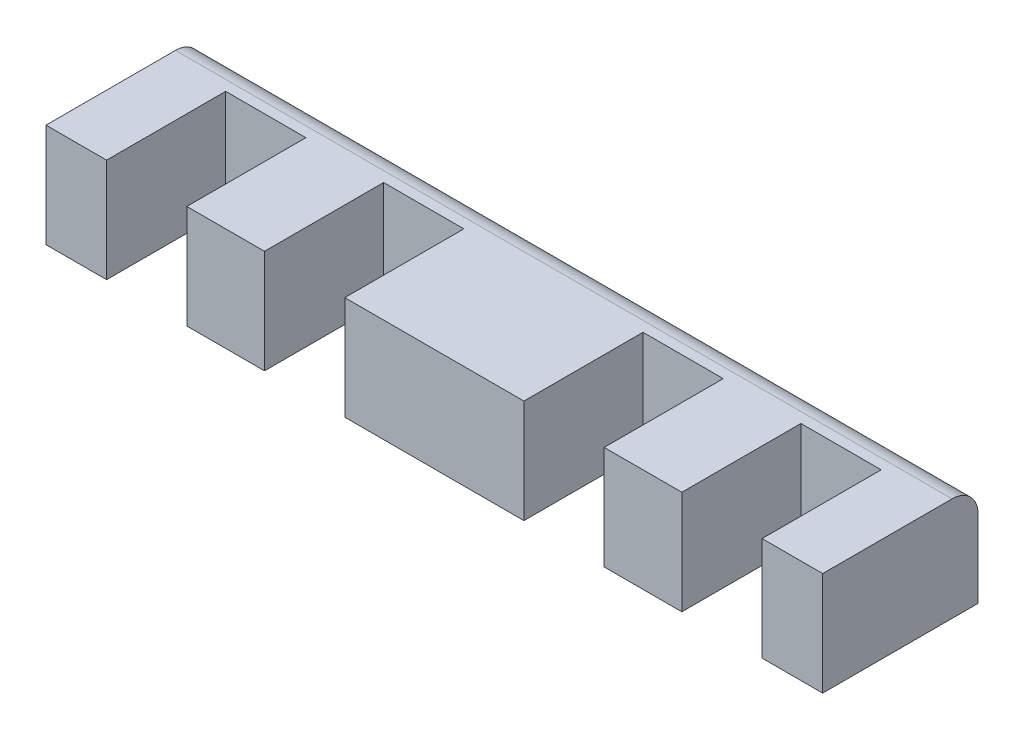
SolidWorks part; units mm, degrees
ref_plane "Front Plane" through (0, 0, 0) normal (0, 0, 1) x (1, 0, 0)
ref_plane "Top Plane" through (0, 0, 0) normal (0, 1, 0) x (1, 0, 0)
ref_plane "Right Plane" through (0, 0, 0) normal (1, 0, 0) x (0, 0, -1)
sketch "Sketch1" plane through (0, 0, 0) normal (0, 1, 0) x (1, 0, 0)
  line L1 (-75, -15) -> (75, -15)
  line L2 (-75, -15) -> (-75, 15)
  line L3 (-75, 15) -> (75, 15)
  line L4 (75, -15) -> (75, 15)
  line L5 (-75, -15) -> (75, 15) construction
  line L6 (-75, 15) -> (75, -15) construction
  line L7 (-63.3, -15) -> (-47.8, -15)
  line L8 (-63.3, -15) -> (-63.3, 8)
  line L9 (-63.3, 8) -> (-47.8, 8)
  line L10 (-47.8, -15) -> (-47.8, 8)
  line L11 (-32.8, -15) -> (-17.3, -15)
  line L12 (-32.8, -15) -> (-32.8, 8)
  line L13 (-32.8, 8) -> (-17.3, 8)
  line L14 (-17.3, -15) -> (-17.3, 8)
  line L15 (63.3, -15) -> (47.8, -15)
  line L16 (63.3, -15) -> (63.3, 8)
  line L17 (63.3, 8) -> (47.8, 8)
  line L18 (47.8, -15) -> (47.8, 8)
  line L19 (32.8, -15) -> (17.3, -15)
  line L20 (32.8, -15) -> (32.8, 8)
  line L21 (32.8, 8) -> (17.3, 8)
  line L22 (17.3, -15) -> (17.3, 8)
  point P0 (0, 0)
  dimension "D1" = 30
  dimension "D2" = 150
  dimension "D3" = 23
  dimension "D4" = 15.5
  dimension "D5" = 11.7
  dimension "D6" = 23
  dimension "D7" = 15.5
  dimension "D8" = 15
  dimension "D9" = 15.5
  dimension "D10" = 23
  dimension "D11" = 11.7
  dimension "D12" = 15.5
  dimension "D13" = 23
  dimension "D14" = 15
extrude "Boss-Extrude1" add sketch "Sketch1" along normal blind 20 contours L1 L22 L21 L20 L18 L17 L16 L4 L3 L2 L8 L9 L10 L12 L13 L14
fillet "Fillet1" radius 5 1 edges at (0, 20, -15)
